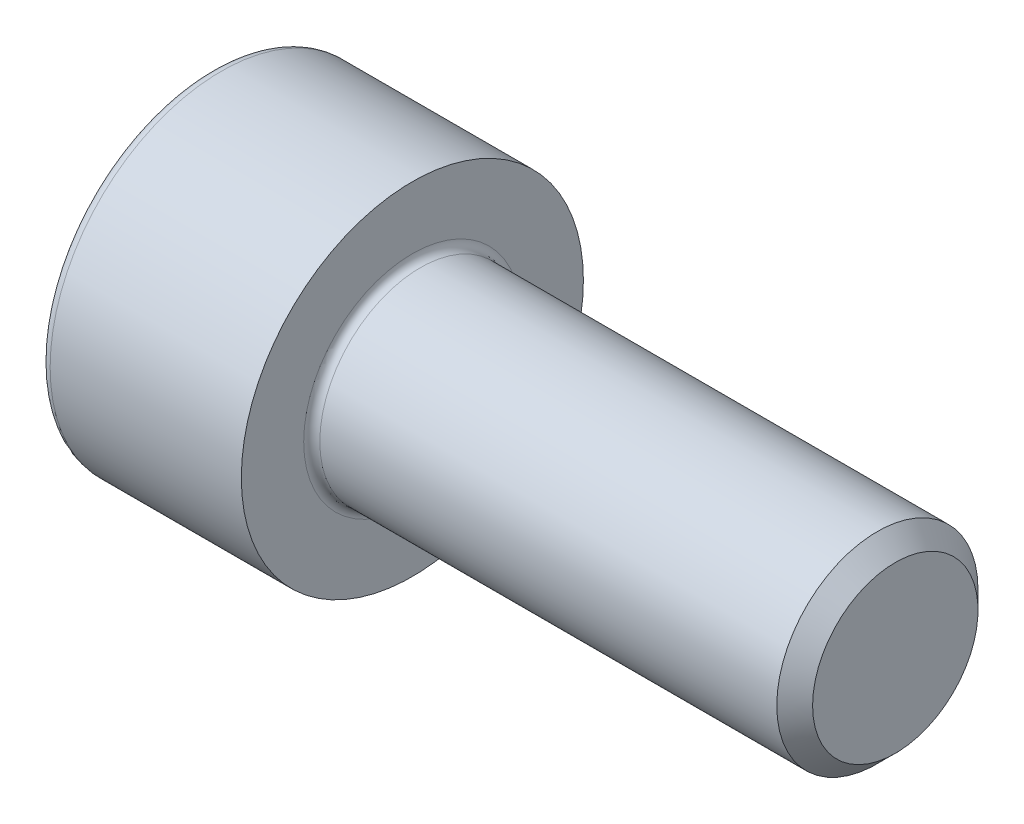
SolidWorks part; units mm, degrees
ref_plane "Plane1" through (0, 0, 0) normal (0, 0, 1) x (1, 0, 0)
ref_plane "Plane2" through (0, 0, 0) normal (0, 1, 0) x (1, 0, 0)
ref_plane "Plane3" through (0, 0, 0) normal (1, 0, 0) x (0, 0, -1)
sketch "BodySke" plane through (0, 0, 0) normal (0, 0, 1) x (1, 0, 0)
  line L0 (0, 0) -> (0, 4.25)
  line L1 (0, 4.25) -> (5, 4.25)
  line L2 (5, 4.25) -> (5, 2.5)
  line L3 (5, 2.5) -> (16.555, 2.5)
  line L4 (17, 2.055) -> (17, 0)
  line L5 (17, 0) -> (0, 0)
  line L6 (-31.75, 0) -> (127, 0) construction
  line L8 (17, 2.055) -> (16.555, 2.5)
  line L10 (17, -2.055) -> (16.555, -2.5) construction
  line L11 (5.8, 9.525) -> (5.8, 3.175) construction
  line L12 (5, 9.525) -> (5, 3.175) construction
  line L13 (-43, 9.525) -> (-43, 3.175) construction
  dimension "Diameter" = 5
  dimension "Head_ht" = 5
  dimension "Length" = 12
  dimension "Body_ch_ang" = 45
  dimension "Head_dia" = 8.5
  dimension "Minor_dia" = 4.11
  dimension "Advance" = 0.8
  dimension "Thread_nom" = 12
  dimension "Thread_length" = 60
revolve "Base-Revolve" add sketch "BodySke"
cosmetic thread "ThreadCosmetic" [suppressed]
fillet "Fillet1" radius 0.2 1 edges at (5, 0, 2.5)
fillet "Fillet2" radius 0.25 1 edges at (0, 0, 4.25)
sketch "Sketch2" plane through (0, 0, 0) normal (0, 0, 1) x (1, 0, 0)
  line L0 (0, 2.042) -> (2.5, 2.042)
  line L1 (2.5, 2.042) -> (3.6789, 0)
  line L2 (-31.75, 0) -> (127, 0) construction
  line L3 (3.6789, 0) -> (0, 0)
  line L4 (0, 0) -> (0, 2.042)
  line L6 (0, 0) -> (47.625, 0) construction
  dimension "D1" = 2.042
  dimension "D2" = 60
  dimension "Depth" = 2.5
revolve "Hex-PreBroach" cut sketch "Sketch2" angle 360 about L6
sketch "Sketch3" plane through (0, 0, 0) normal (-1, 0, 0) x (0, 0.5, 0.866)
  line L0 (1.1789, 2.042) -> (-1.1789, 2.042)
  line L1 (-1.1789, 2.042) -> (-2.3579, 0)
  line L2 (1.1789, 2.042) -> (2.3579, 0)
  line L3 (1.1789, -2.042) -> (2.3579, 0)
  line L4 (1.1789, -2.042) -> (-1.1789, -2.042)
  line L5 (-1.1789, -2.042) -> (-2.3579, 0)
  dimension "D1" = 2.042
  dimension "D2" = 2.042
  dimension "Hex_size" = 4.084
extrude "Hex" cut sketch "Sketch3" against normal blind 2.5
sketch "ThdSchSke" plane through (0, 0, 0) normal (0, 0, 1) x (1, 0, 0)
  line L0 (7.4, -2.055) -> (7.0884, -2.5)
  line L1 (7.4, -2.055) -> (7.7116, -2.5)
  line L2 (7.7116, -2.5) -> (7.7116, -3.125)
  line L3 (-3.175, 0) -> (5.1513, 0) construction
  line L4 (0, 4) -> (0, -4) construction
  line L5 (7.7116, -3.125) -> (7.0884, -3.125)
  line L6 (7.0884, -3.125) -> (7.0884, -2.5)
  dimension "Thread_minor" = 4.11
  dimension "Diameter" = 5
  dimension "Start" = 7.4
  dimension "SideAngle" = 55
  dimension "VeeAngle" = 70
  dimension "Overcut" = 6.25
revolve "ThreadSchematic" [suppressed] cut sketch "ThdSchSke" angle 360 about L3
pattern_linear "ThdSchPat" [suppressed]
equation "\"D2@Sketch3\" = \"Hex_size@Sketch3\" / 2"
equation "\"D1@Sketch3\" = \"Hex_size@Sketch3\" / 2"
equation "\"D1@Sketch2\" = \"Hex_size@Sketch3\" / 2"
equation "\"Thread_minor@ThreadCosmetic\"  =  \"Minor_dia@BodySke\""
equation "\"Depth@Sketch2\" =  \"Key_eng@Hex\""
equation "\"Thread_length@ThreadCosmetic\" = ((sgn( (\"Length@BodySke\" - \"Advance@BodySke\" * 3.0) - \"Thread_nom@BodySke\" )-1)*( (\"Length@BodySke\" - \"Advance@BodySke\" * 3.0) - \"Thread_nom@BodySke\" ))/-2+ \"Thread_nom@BodySke\""
equation "\"Thread_minor@ThdSchSke\" = \"Minor_dia@BodySke\""
equation "\"Diameter@ThdSchSke\" = \"Diameter@BodySke\""
equation "\"Overcut@ThdSchSke\" = \"Diameter@BodySke\" * 1.25"
equation "\"Start@ThdSchSke\" = \"Head_ht@BodySke\" + \"Length@BodySke\" - \"Thread_length@ThreadCosmetic\"  '---Non-countersunk---"
equation "\"Num_threads@ThdSchPat\" = int( \"Thread_length@ThreadCosmetic\" / \"Advance@BodySke\" + 0.999 )  + 1"
equation "\"Advance@ThdSchPat\" = \"Thread_length@ThreadCosmetic\" /  (\"Num_threads@ThdSchPat\" - 1) 'relax it"
equation "\"Num_threads@ThdSchPat\" = \"Num_threads@ThdSchPat\" - sgn( \"Num_threads@ThdSchPat\" - 1) '---chamfered tips only---"
